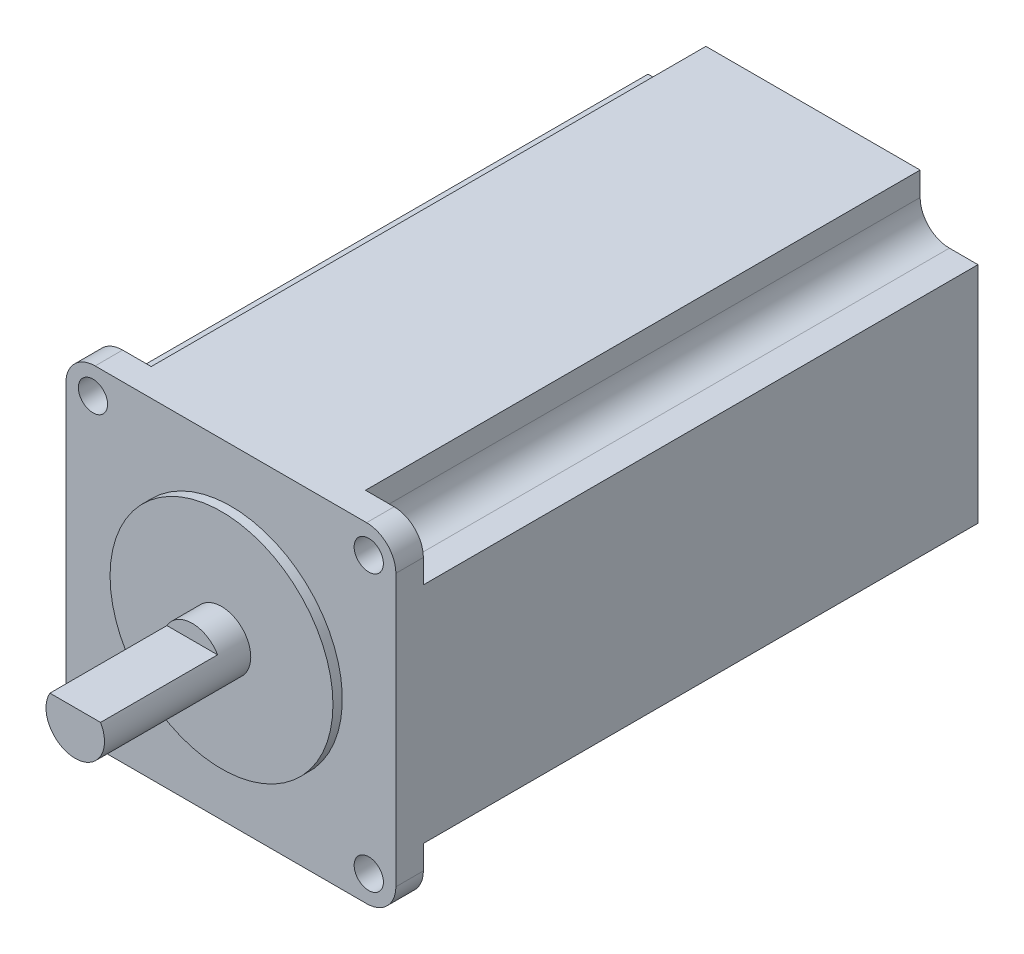
SolidWorks part; units mm, degrees
ref_plane "前视基准面" through (0, 0, 0) normal (0, 0, 1) x (1, 0, 0)
ref_plane "上视基准面" through (0, 0, 0) normal (0, 1, 0) x (1, 0, 0)
ref_plane "右视基准面" through (0, 0, 0) normal (1, 0, 0) x (0, 0, -1)
sketch "草图1" plane through (0, 0, 0) normal (0, 0, 1) x (1, 0, 0)
  line L1 (0, 0) -> (56.4, 0)
  line L2 (0, 0) -> (0, 56.4)
  line L3 (0, 56.4) -> (56.4, 56.4)
  line L4 (56.4, 0) -> (56.4, 56.4)
  dimension "D1" = 56.4
  dimension "D2" = 56.4
extrude "凸台-拉伸1" add sketch "草图1" along normal blind 99.5
sketch "草图2" plane through (0, 0, 99.5) normal (0, 0, 1) x (1, 0, 0)
  line L0 (28.2, 56.4) -> (28.2, 0) construction
  line L1 (56.4, 56.4) -> (0, 56.4) construction
  line L2 (0, 0) -> (56.4, 0) construction
  line L3 (28.2, 0) -> (28.2, 28.2) construction
  circle A0 centre (28.2, 28.2) radius 19.05
  dimension "D1" = 38.1
extrude "凸台-拉伸2" add sketch "草图2" along normal blind 1.6
sketch "草图3" plane through (0, 0, 101.1) normal (0, 0, 1) x (1, 0, 0)
  line L0 (28.2, 28.2) -> (28.2, 56.4) construction
  line L1 (56.4, 56.4) -> (0, 56.4) construction
  circle A0 centre (28.2, 28.2) radius 5
  dimension "D1" = 10
extrude "凸台-拉伸3" add sketch "草图3" along normal blind 25
sketch "草图4" plane through (0, 0, 126.1) normal (0, 0, 1) x (1, 0, 0)
  line L0 (28.2, 28.2) -> (28.2, 56.4) construction
  line L1 (56.4, 56.4) -> (0, 56.4) construction
  line L3 (23.8699, 36.7292) -> (32.5301, 36.7292)
  line L4 (23.8699, 36.7292) -> (23.8699, 30.7)
  line L5 (23.8699, 30.7) -> (32.5301, 30.7)
  line L6 (32.5301, 36.7292) -> (32.5301, 30.7)
  circle A0 centre (28.2, 28.2) radius 5 construction
  dimension "D1" = 2.5
extrude "切除-拉伸1" cut sketch "草图4" against normal blind 20
sketch "草图5" plane through (0, 0, 0) normal (0, 0, -1) x (-1, 0, 0)
  line L0 (-28.2, 56.4) -> (-28.2, 0) construction
  line L1 (-61.9888, 58.0625) -> (-46.5101, 58.0625)
  line L2 (-61.9888, 58.0625) -> (-61.9888, 47.3407)
  line L3 (-61.9888, 47.3407) -> (-51.5101, 47.3407)
  line L4 (-46.5101, 58.0625) -> (-46.5101, 52.3407)
  line L5 (-56.4, 56.4) -> (0, 56.4) construction
  line L6 (0, 0) -> (-56.4, 0) construction
  line L7 (-28.2, 0) -> (-28.2, 28.2) construction
  line L8 (-28.2, 28.2) -> (6.4949, 28.2) construction
  line L9 (-9.8899, 58.0625) -> (-9.8899, 52.3407)
  line L10 (5.5888, 47.3407) -> (-4.8899, 47.3407)
  line L11 (5.5888, 58.0625) -> (-9.8899, 58.0625)
  line L12 (5.5888, 58.0625) -> (5.5888, 47.3407)
  line L13 (5.5888, -1.6625) -> (-9.8899, -1.6625)
  line L14 (5.5888, -1.6625) -> (5.5888, 9.0593)
  line L15 (5.5888, 9.0593) -> (-4.8899, 9.0593)
  line L16 (-9.8899, -1.6625) -> (-9.8899, 4.0593)
  line L17 (-46.5101, -1.6625) -> (-46.5101, 4.0593)
  line L18 (-61.9888, -1.6625) -> (-46.5101, -1.6625)
  line L19 (-61.9888, -1.6625) -> (-61.9888, 9.0593)
  line L20 (-61.9888, 9.0593) -> (-51.5101, 9.0593)
  arc A0 (-51.5101, 47.3407) -> (-46.5101, 52.3407) centre (-51.5101, 52.3407) ccw
  arc A1 (-4.8899, 47.3407) -> (-9.8899, 52.3407) centre (-4.8899, 52.3407) cw
  arc A2 (-4.8899, 9.0593) -> (-9.8899, 4.0593) centre (-4.8899, 4.0593) ccw
  arc A3 (-51.5101, 9.0593) -> (-46.5101, 4.0593) centre (-51.5101, 4.0593) cw
  dimension "D1" = 5
extrude "切除-拉伸2" cut sketch "草图5" against normal blind 94.8
sketch "草图6" plane through (0, 0, 99.5) normal (0, 0, 1) x (1, 0, 0)
  line L0 (28.2, 56.4) -> (28.2, 0) construction
  line L1 (56.4, 56.4) -> (0, 56.4) construction
  line L2 (0, 0) -> (56.4, 0) construction
  line L3 (28.2, 0) -> (28.2, 28.2) construction
  line L4 (28.2, 28.2) -> (68.6333, 28.2) construction
  circle A0 centre (4.63, 51.77) radius 2.5
  circle A1 centre (51.77, 51.77) radius 2.5
  circle A2 centre (51.77, 4.63) radius 2.5
  circle A3 centre (4.63, 4.63) radius 2.5
  dimension "D1" = 5
  dimension "D2" = 47.14
  dimension "D3" = 47.14
extrude "切除-拉伸3" cut sketch "草图6" against normal blind 94.8
fillet "圆角1" radius 5 4 edges at (0, 0, 97.15) (56.4, 0, 97.15) (0, 56.4, 97.15) (56.4, 56.4, 97.15)
